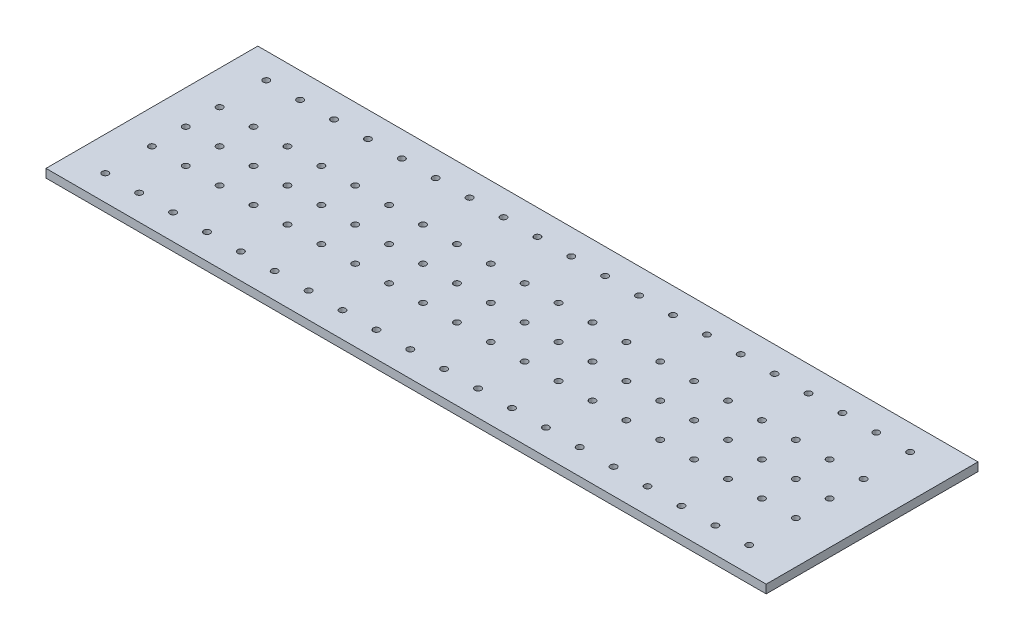
SolidWorks part; units mm, degrees
ref_plane "Front Plane" through (0, 0, 0) normal (0, 0, 1) x (1, 0, 0)
ref_plane "Top Plane" through (0, 0, 0) normal (0, 1, 0) x (1, 0, 0)
ref_plane "Right Plane" through (0, 0, 0) normal (1, 0, 0) x (0, 0, -1)
sketch "Sketch1" plane through (0, 0, 0) normal (0, 1, 0) x (1, 0, 0)
  line L1 (-425, 125) -> (425, 125)
  line L2 (-425, 125) -> (-425, -125)
  line L3 (-425, -125) -> (425, -125)
  line L4 (425, 125) -> (425, -125)
  line L5 (-425, 125) -> (425, -125) construction
  line L6 (-425, -125) -> (425, 125) construction
  point P0 (0, 0)
  dimension "D1" = 850
  dimension "D2" = 250
extrude "Boss-Extrude1" add sketch "Sketch1" along normal blind 10
sketch "Sketch2" plane through (0, 10, 0) normal (0, 1, 0) x (1, 0, 0)
  line L0 (-1275.6387, 95) -> (48724.3613, 95) construction
  line L1 (-1258.6746, -95) -> (48741.3254, -95) construction
  line L2 (-385.0573, -979.1357) -> (-385.0573, 49020.8643) construction
  line L3 (-1000, 0) -> (49000, 0) construction
  line L4 (425, 125) -> (-425, 125) construction
  line L5 (-425, -125) -> (425, -125) construction
  line L6 (-1425, 40) -> (48575, 40) construction
  line L8 (-1425, -40) -> (48575, -40) construction
  circle A0 centre (-385.0573, 95) radius 3.75
  circle A1 centre (-385.0573, 0) radius 3.75
  circle A2 centre (-385.0573, -95) radius 3.75
  circle A3 centre (-385.0573, 40) radius 3.75
  circle A4 centre (-385.0573, -40) radius 3.75
  dimension "D3" = 95
  dimension "D1" = 30
  dimension "D2" = 30
  dimension "D4" = 40
  dimension "D5" = 40
extrude "Cut-Extrude1" cut sketch "Sketch2" against normal up to next (10 mm away)
pattern_linear "LPattern1" count 20 spacing 40 along (1, 0, 0) of "Cut-Extrude1"
